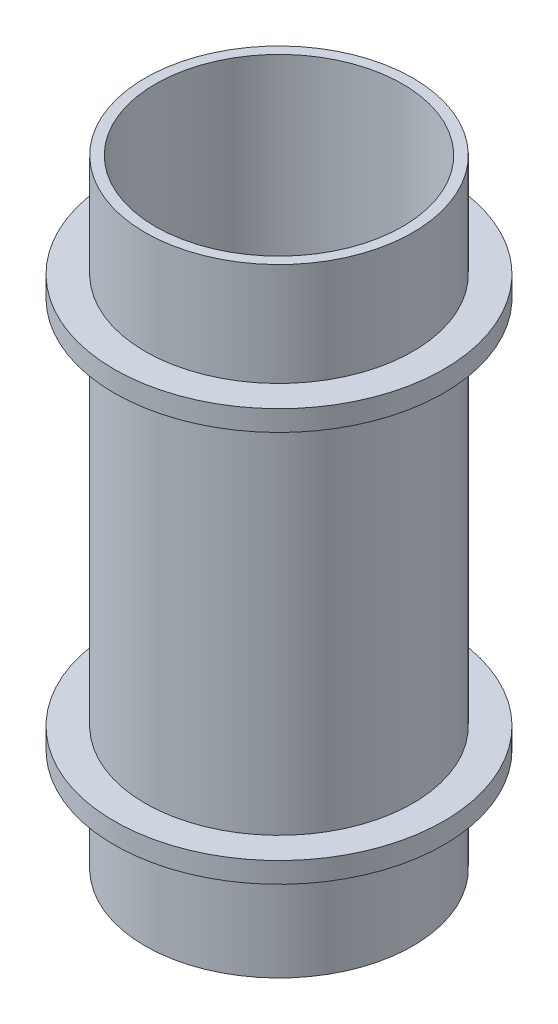
SolidWorks part; units mm, degrees
ref_plane "Спереди" through (0, 0, 0) normal (0, 0, 1) x (1, 0, 0)
ref_plane "Сверху" through (0, 0, 0) normal (0, 1, 0) x (1, 0, 0)
ref_plane "Справа" through (0, 0, 0) normal (1, 0, 0) x (0, 0, -1)
other "Центр тяжести"
sketch "Эскиз1" plane through (0, 0, 0) normal (0, 1, 0) x (1, 0, 0)
  circle A0 centre (0, 0) radius 12
  circle A1 centre (0, 0) radius 13
  dimension "D1" = 24
  dimension "D2" = 26
extrude "Бобышка-Вытянуть1" add sketch "Эскиз1" along normal blind 60
sketch "Эскиз2" plane through (0, 60, 0) normal (0, 1, 0) x (1, 0, 0)
  circle A1 centre (0, 0) radius 16
  circle A3 centre (0, 0) radius 12
  dimension "D1" = 32
  dimension "D2" = 24
extrude "Бобышка-Вытянуть3" add sketch "Эскиз2" against normal blind 2 from offset 10 offset against normal yes
sketch "Эскиз3" plane through (0, 0, 0) normal (0, -1, 0) x (1, 0, 0)
  circle A0 centre (0, 0) radius 12
  circle A1 centre (0, 0) radius 16
  dimension "D1" = 24
extrude "Бобышка-Вытянуть4" add sketch "Эскиз3" against normal blind 2 from offset 10
